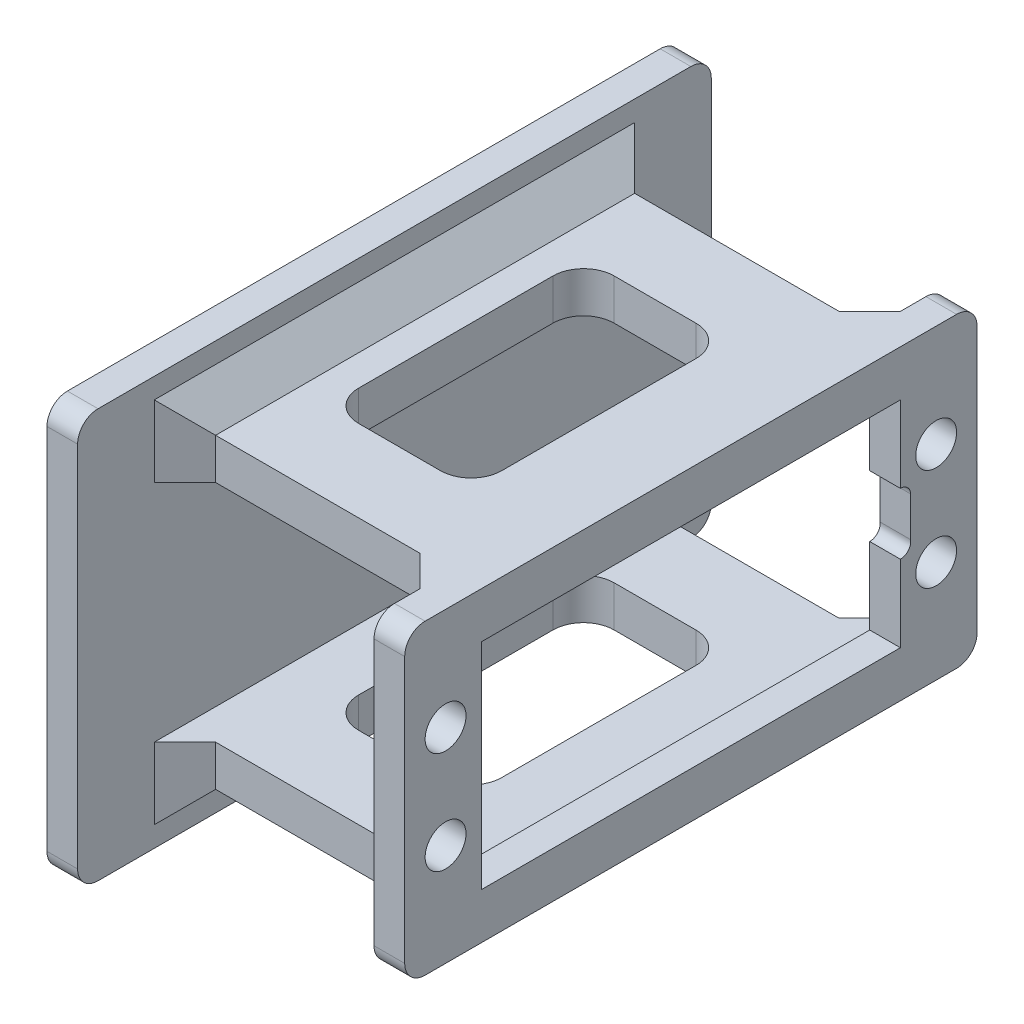
SolidWorks part; units mm, degrees
ref_plane "Спереди" through (0, 0, 0) normal (0, 0, 1) x (1, 0, 0)
ref_plane "Сверху" through (0, 0, 0) normal (0, 1, 0) x (1, 0, 0)
ref_plane "Справа" through (0, 0, 0) normal (1, 0, 0) x (0, 0, -1)
sketch "Эскиз1" plane through (0, 0, 0) normal (1, 0, 0) x (0, 0, -1)
  line L0 (-20.5, 21) -> (-20.5, 25.5) construction
  line L1 (0, 0) -> (-41, 0)
  line L2 (0, 0) -> (0, 7.5001)
  line L3 (0, 21) -> (-41, 21)
  line L4 (-41, 0) -> (-41, 21)
  line L5 (7.5, 25.5) -> (-48.5, 25.5)
  line L6 (7.5, 25.5) -> (7.5, -4.5)
  line L7 (7.5, -4.5) -> (-48.5, -4.5)
  line L8 (-48.5, 25.5) -> (-48.5, -4.5)
  line L9 (3.5, 25.5) -> (3.5, -4.5) construction
  line L10 (1, 10.5) -> (7.5, 10.5) construction
  line L11 (0, 13.4999) -> (0, 10.5) construction
  line L12 (-44.5, 25.5) -> (-44.5, -4.5) construction
  line L13 (3.5, 15.5) -> (-44.5, 15.5) construction
  line L14 (1, 12.5332) -> (1, 8.6637)
  line L15 (3.5, 5.5) -> (-44.5, 5.5) construction
  line L16 (0, 10.5) -> (1, 10.5) construction
  line L17 (0, 13.4999) -> (0, 21)
  line L18 (0, 10.5) -> (0, 7.5001) construction
  circle A0 centre (3.5, 15.5) radius 2
  circle A1 centre (3.5, 5.5) radius 2
  circle A2 centre (-44.5, 5.5) radius 2
  circle A3 centre (-44.5, 15.5) radius 2
  arc A4 (1, 12.5332) -> (0, 13.4999) centre (0.0006, 12.4999) ccw
  arc A5 (0, 7.5001) -> (1, 8.6637) centre (0.0135, 8.5) ccw
  point P4 (0, 0)
  point P28 (0, 10.5)
  point P32 (0, 10.5381)
  point P33 (0, 0)
  point P34 (0, 0)
  point P35 (0, 10.5381)
  point P36 (0, 0)
  dimension "D8" = 4
  dimension "D10" = 1
  dimension "D1" = 21
  dimension "D2" = 41
  dimension "D3" = 48
  dimension "D4" = 24
  dimension "D5" = 56
  dimension "D6" = 10
  dimension "D7" = 5
  dimension "D9" = 30
  dimension "D11" = 4
  dimension "D12" = 1
extrude "Бобышка-Вытянуть1" add sketch "Эскиз1" along normal blind 3
sketch "Эскиз2" plane through (0, 0, 0) normal (-1, 0, 0) x (0, 0, 1)
  line L0 (-7.5, 25.5) -> (48.5, 25.5) construction
  line L1 (0, 25.5) -> (41, 25.5)
  line L2 (0, 25.5) -> (0, 21.5)
  line L3 (0, 21.5) -> (41, 21.5)
  line L4 (41, 25.5) -> (41, 21.5)
  line L5 (48.5, -4.5) -> (-7.5, -4.5) construction
  line L6 (0, -4.5) -> (41, -4.5)
  line L7 (0, -4.5) -> (0, -0.5)
  line L8 (0, -0.5) -> (41, -0.5)
  line L9 (41, -4.5) -> (41, -0.5)
  line L10 (0, 21.5) -> (0, 21) construction
  line L11 (41, 21.5) -> (41, 21) construction
  line L12 (0, -0.5) -> (0, 0) construction
  line L13 (41, -0.5) -> (41, 0) construction
  dimension "D1" = 4
  dimension "D2" = 4
extrude "Бобышка-Вытянуть2" add sketch "Эскиз2" along normal blind 26
sketch "Эскиз3" plane through (-26, 0, 0) normal (-1, 0, 0) x (0, 0, 1)
  line L0 (41, 25.5) -> (0, 25.5) construction
  line L1 (-10.5, 30.5) -> (51.5, 30.5)
  line L2 (-10.5, 30.5) -> (-10.5, -9.5)
  line L3 (-10.5, -9.5) -> (51.5, -9.5)
  line L4 (51.5, 30.5) -> (51.5, -9.5)
  line L5 (0, -4.5) -> (41, -4.5) construction
  line L6 (-7.5, -4.5) -> (-7.5, 25.5) construction
  line L7 (48.5, 25.5) -> (48.5, -4.5) construction
  point P8 (-8.7076, 30.5)
  dimension "D1" = 5
  dimension "D2" = 5
  dimension "D3" = 3
  dimension "D4" = 3
extrude "Бобышка-Вытянуть3" add sketch "Эскиз3" along normal blind 3
chamfer "Фаска2" distance 3 angle 45 2 edges at (-26, 25.5, 20.5) (-26, -4.5, 20.5)
sketch "Эскиз4" plane through (0, -4.5, 0) normal (0, -1, 0) x (1, 0, 0)
  line L1 (-17, 33) -> (-9, 33)
  line L2 (-20, 30) -> (-20, 11)
  line L3 (-17, 8) -> (-9, 8)
  line L4 (-6, 30) -> (-6, 11)
  line L5 (-26, -10.5) -> (-26, 51.5) construction
  line L6 (0, 48.5) -> (0, 41) construction
  line L7 (-23, 0) -> (0, 0) construction
  line L8 (-23, 41) -> (0, 41) construction
  arc A0 (-20, 11) -> (-17, 8) centre (-17, 11) ccw
  arc A1 (-9, 8) -> (-6, 11) centre (-9, 11) ccw
  arc A2 (-9, 33) -> (-6, 30) centre (-9, 30) cw
  arc A3 (-17, 33) -> (-20, 30) centre (-17, 30) ccw
  point P8 (0, 44.75)
  dimension "D5" = 3
  dimension "D1" = 6
  dimension "D2" = 6
  dimension "D3" = 8
  dimension "D4" = 8
extrude "Вырез-Вытянуть1" cut sketch "Эскиз4" against normal through all
fillet "Скругление1" radius 2 8 edges at (-27.5, 30.5, 51.5) (-27.5, -9.5, 51.5) (1.5, -4.5, 48.5) (1.5, 25.5, 48.5) (1.5, 25.5, -7.5) (1.5, -4.5, -7.5) (-27.5, 30.5, -10.5) (-27.5, -9.5, -10.5)
chamfer "Фаска3" distance 3 angle 45 4 edges at (0, 23.5, 41) (0, -2.5, 41) (0, -2.5, 0) (0, 23.5, 0)
chamfer "Фаска4" distance 3 angle 45 4 edges at (-26, 25, 0) (-26, -4, 0) (-26, 25, 41) (-26, -4, 41)
